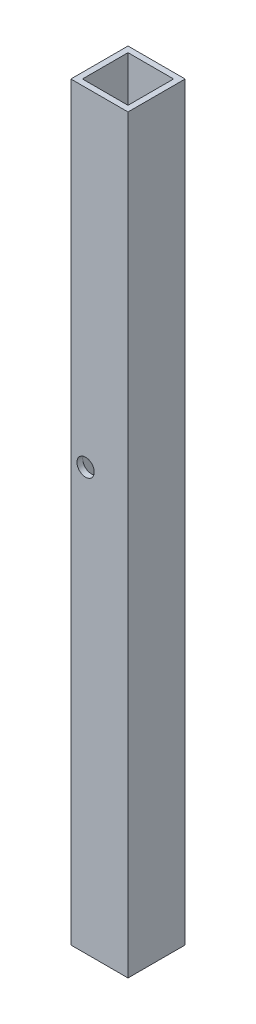
SolidWorks part; units mm, degrees
ref_plane "Спереди" through (0, 0, 0) normal (0, 0, 1) x (1, 0, 0)
ref_plane "Сверху" through (0, 0, 0) normal (0, 1, 0) x (1, 0, 0)
ref_plane "Справа" through (0, 0, 0) normal (1, 0, 0) x (0, 0, -1)
sketch "Эскиз1" plane through (0, 0, 0) normal (0, 1, 0) x (1, 0, 0)
  line L1 (4.95, -4.95) -> (-4.95, -4.95)
  line L2 (4.95, -4.95) -> (4.95, 4.95)
  line L3 (4.95, 4.95) -> (-4.95, 4.95)
  line L4 (-4.95, -4.95) -> (-4.95, 4.95)
  line L5 (-3.95, -3.95) -> (3.95, -3.95)
  line L6 (-3.95, -3.95) -> (-3.95, 3.95)
  line L7 (-3.95, 3.95) -> (3.95, 3.95)
  line L8 (3.95, -3.95) -> (3.95, 3.95)
  line L9 (-3.95, -3.95) -> (3.95, 3.95) construction
  line L10 (-3.95, 3.95) -> (3.95, -3.95) construction
  point P0 (0, 0)
  point P6 (0, 0)
  point P7 (0, 0)
  point P16 (2.2052, -0.1083)
  dimension "D3" = 1
  dimension "D5" = 1
  dimension "D1" = 1
  dimension "D2" = 9.9
  dimension "D4" = 1
extrude "Бобышка-Вытянуть1" add sketch "Эскиз1" along normal blind 130
sketch "Sketch2" plane through (0, 0, -4.95) normal (0, 0, -1) x (-1, 0, 0)
  line L0 (0, 130) -> (0, 0) construction
  line L1 (-4.95, 130) -> (4.95, 130) construction
  line L2 (-4.95, 0) -> (4.95, 0) construction
  line L3 (2.4, 0) -> (2.4, 130) construction
  line L4 (-4.95, 73) -> (3.9, 73) construction
  line L5 (-4.95, 130) -> (-4.95, 0) construction
  circle A0 centre (0, 125) radius 1.5 construction
  circle A1 centre (2.4, 73) radius 1.5
  circle A2 centre (0, 105) radius 1.5 construction
  dimension "D2" = 3
  dimension "D3" = 2.4
  dimension "D1" = 5
  dimension "D4" = 52
  dimension "D5" = 20
extrude "Cut-Extrude2" cut sketch "Sketch2" against normal through all
